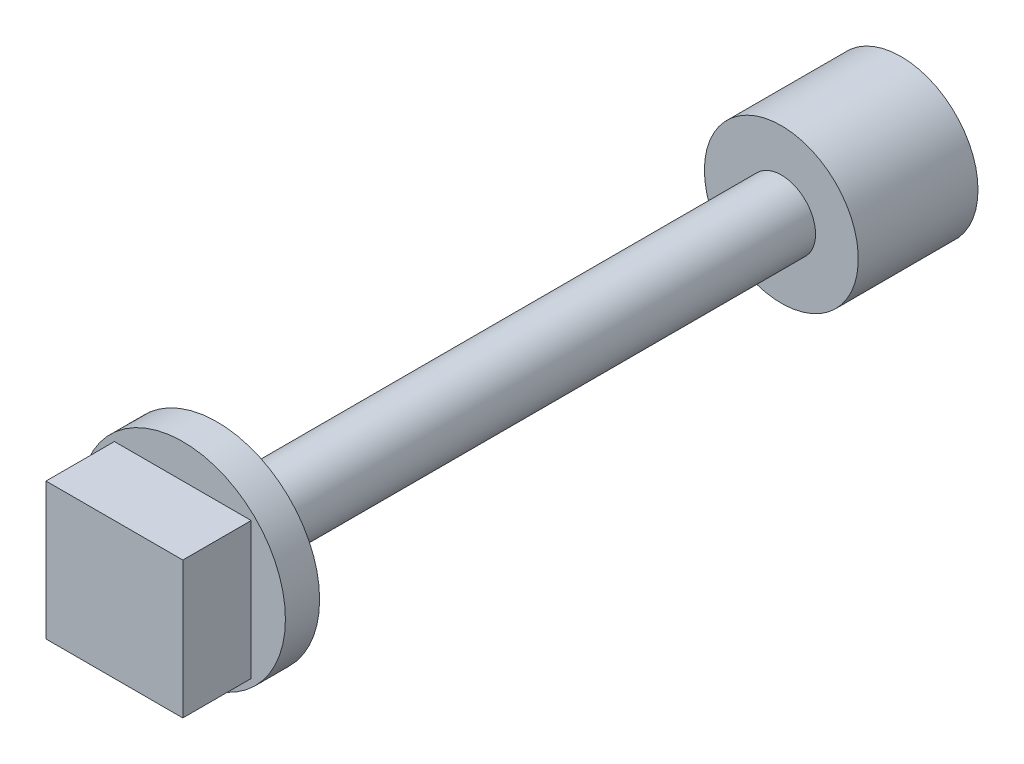
SolidWorks part; units mm, degrees
ref_plane "Front Plane" through (0, 0, 0) normal (0, 0, 1) x (1, 0, 0)
ref_plane "Top Plane" through (0, 0, 0) normal (0, 1, 0) x (1, 0, 0)
ref_plane "Right Plane" through (0, 0, 0) normal (1, 0, 0) x (0, 0, -1)
sketch "草图1" plane through (0, 0, 0) normal (0, 0, 1) x (1, 0, 0)
  circle A0 centre (0, 0) radius 2.25
  dimension "D1" = 4.5
extrude "凸台-拉伸2" add sketch "草图1" along normal blind 20
sketch "草图7" plane through (0, 0, 0) normal (0, 0, 1) x (1, 0, 0)
  line L1 (1.2, -1.2) -> (-1.2, -1.2)
  line L2 (1.2, -1.2) -> (1.2, 1.2)
  line L3 (1.2, 1.2) -> (-1.2, 1.2)
  line L4 (-1.2, -1.2) -> (-1.2, 1.2)
  line L5 (1.2, -1.2) -> (-1.2, 1.2) construction
  line L6 (1.2, 1.2) -> (-1.2, -1.2) construction
  point P0 (0, 0)
  dimension "D1" = 2.4
  dimension "D2" = 2.4
extrude "切除-拉伸3" cut sketch "草图7" along normal blind 2.5 from surface at 0 starting at face at (2.25, 0, 0)
sketch "草图9" plane through (0, 0, 20) normal (0, 0, 1) x (1, 0, 0)
  circle A0 centre (0, 0) radius 3
extrude "凸台-拉伸4" add sketch "草图9" along normal blind 1
sketch "草图10" plane through (0, 0, 21) normal (0, 0, 1) x (1, 0, 0)
  line L1 (2, -2) -> (-2, -2)
  line L2 (2, -2) -> (2, 2)
  line L3 (2, 2) -> (-2, 2)
  line L4 (-2, -2) -> (-2, 2)
  line L5 (2, -2) -> (-2, 2) construction
  line L6 (2, 2) -> (-2, -2) construction
  point P0 (0, 0)
  dimension "D1" = 4
  dimension "D2" = 4
extrude "凸台-拉伸5" add sketch "草图10" along normal blind 2
sketch "草图12" plane through (0, 0, 0) normal (0, 0, -1) x (-1, 0, 0)
  circle A0 centre (0, 0) radius 1
extrude "切除-拉伸4" cut sketch "草图12" along normal blind 16.5 from surface at -20 flip side to cut starting at face at (2.25, 0, 20)
